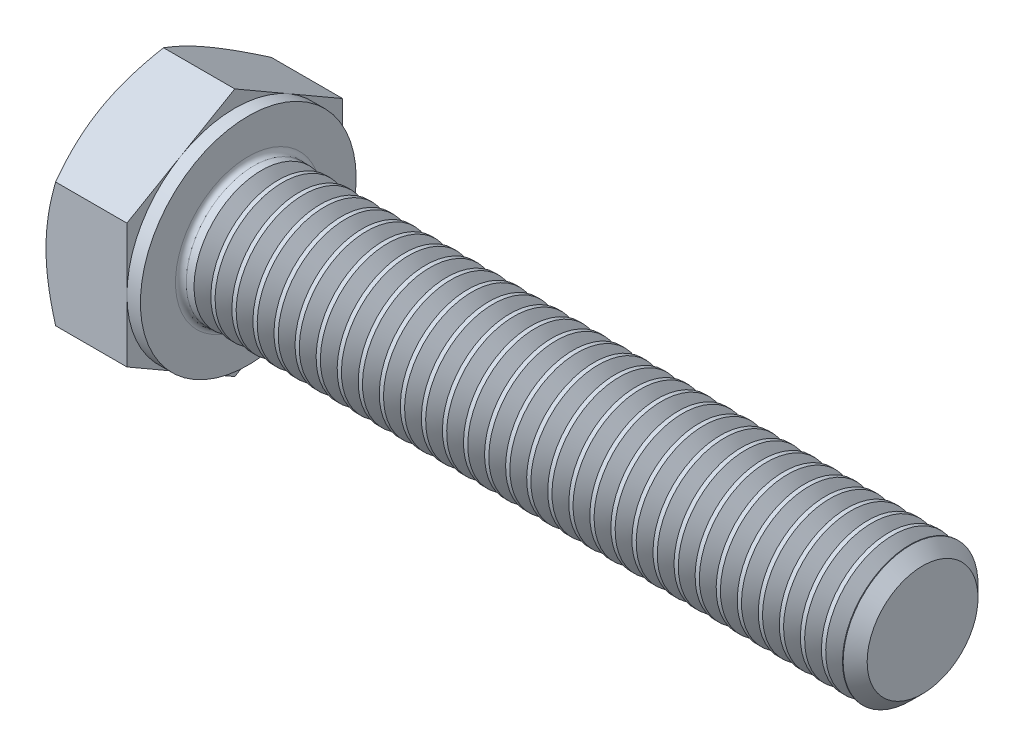
SolidWorks part; units mm, degrees
ref_plane "Plane1" through (0, 0, 0) normal (0, 0, 1) x (1, 0, 0)
ref_plane "Plane2" through (0, 0, 0) normal (0, 1, 0) x (1, 0, 0)
ref_plane "Plane3" through (0, 0, 0) normal (1, 0, 0) x (0, 0, -1)
sketch "Sketch1" plane through (0, 0, 0) normal (1, 0, 0) x (0, 0, -1)
  line L0 (4, 2.3094) -> (4, -2.3094)
  line L1 (-4, 2.3094) -> (-4, -2.3094)
  line L2 (4, -2.3094) -> (0, -4.6188)
  line L3 (0, -4.6188) -> (-4, -2.3094)
  line L4 (4, 2.3094) -> (0, 4.6188)
  line L5 (0, 4.6188) -> (-4, 2.3094)
  dimension "Width_flats" = 8
  dimension "D2" = 120
  dimension "D3" = 4
  dimension "D4" = 4
  dimension "D5" = 4
extrude "BaseHead" add sketch "Sketch1" along normal blind 3.5
sketch "BodySke" plane through (0, 0, 0) normal (0, 0, 1) x (1, 0, 0)
  line L0 (0, 2.3094) -> (0, -2.3094) construction
  line L1 (0, 0) -> (28.5, 0)
  line L2 (0, 0) -> (0, 2.5)
  line L3 (0, 2.5) -> (28.055, 2.5)
  line L4 (28.5, 0) -> (28.5, 2.055)
  line L5 (3.5, 4.6188) -> (3.5, 2.3094) construction
  line L6 (28.5, 2.055) -> (28.055, 2.5)
  line L7 (0, 0) -> (96.52, 0) construction
  line L8 (28.5, -2.055) -> (28.055, -2.5) construction
  line L9 (0, -2.5) -> (28.055, -2.5) construction
  line L10 (4.3, 15.24) -> (4.3, -1.27) construction
  line L11 (3.5, 15.24) -> (3.5, -1.27) construction
  line L12 (3.5, 2.3094) -> (3.5, -2.3094) construction
  dimension "Length" = 25
  dimension "Body_ch_ang" = 45
  dimension "Diameter" = 5
  dimension "Minor_dia" = 4.11
  dimension "Advance" = 0.8
  dimension "Thread_nom" = 25
revolve "BaseBody" add sketch "BodySke"
cosmetic thread "ThreadCosmetic" [suppressed]
fillet "HeadFillet" radius 0.2 1 edges at (3.5, 0, -2.5)
sketch "Sketch3" plane through (0, 0, 0) normal (0, 0, 1) x (1, 0, 0)
  line L0 (0, 4) -> (3.244, 9.6188)
  line L1 (0, 4.6188) -> (0, 2.3094) construction
  line L2 (3.244, 9.6188) -> (3.244, 14.6188)
  line L3 (3.244, 14.6188) -> (-10, 14.6188)
  line L4 (-10, 14.6188) -> (-10, 4)
  line L5 (-10, 4) -> (0, 4)
  line L6 (0, 0) -> (99.06, 0) construction
  line L7 (3.5, 4.6188) -> (0, 4.6188) construction
  dimension "D1" = 4
  dimension "D2" = 5
  dimension "D3" = 10
  dimension "D4" = 5
  dimension "Head_ch_ang" = 30
revolve "HeadChamfer" cut sketch "Sketch3" angle 360 about L6
sketch "Sketch4" plane through (0, 0, 0) normal (0, 0, 1) x (1, 0, 0)
  line L1 (3.5, 4.6188) -> (3.5, 2.3094) construction
  line L2 (3.5, 4) -> (3, 4)
  line L3 (3.5, 4) -> (3.5, 14.6188)
  line L4 (3.5, 14.6188) -> (3, 14.6188)
  line L5 (0, 0) -> (95.25, 0) construction
  line L6 (0, 0) -> (96.52, 0) construction
  line L7 (3, 4) -> (3, 14.6188)
  line L8 (3.5, 4.6188) -> (0.3573, 4.6188) construction
  dimension "D1" = 8
  dimension "D2" = 10
  dimension "Bearing_ht" = 0.5
revolve "BearingFace" cut sketch "Sketch4" angle 360 about L5
sketch "ThdSchSke" plane through (0, 0, 0) normal (0, 0, 1) x (1, 0, 0)
  line L0 (4.3, -2.055) -> (3.9884, -2.5)
  line L1 (4.3, -2.055) -> (4.6116, -2.5)
  line L2 (4.6116, -2.5) -> (4.6116, -3.125)
  line L3 (-3.175, 0) -> (5.1513, 0) construction
  line L5 (4.6116, -3.125) -> (3.9884, -3.125)
  line L6 (3.9884, -3.125) -> (3.9884, -2.5)
  dimension "Thread_minor" = 4.11
  dimension "Diameter" = 5
  dimension "Start" = 4.3
  dimension "SideAngle" = 55
  dimension "VeeAngle" = 70
  dimension "Overcut" = 6.25
revolve "ThreadSchematic" cut sketch "ThdSchSke" angle 360 about L3
pattern_linear "ThdSchPat" count 31 spacing 0.7806 along (1, 0, 0) of "ThreadSchematic"
equation "\"D3@Sketch1\" = \"Width_flats@Sketch1\" / 2"
equation "\"D4@Sketch1\" = \"D3@Sketch1\""
equation "\"D5@Sketch1\" = \"D4@Sketch1\""
equation "\"Thread_minor@ThreadCosmetic\" = \"Minor_dia@BodySke\""
equation "\"D1@Sketch3\" = \"Width_flats@Sketch1\" / 2"
equation "\"D1@Sketch4\" = \"Width_flats@Sketch1\""
equation "\"Thread_length@ThreadCosmetic\" = ((sgn( (\"Length@BodySke\" - \"Advance@BodySke\" ) - \"Thread_nom@BodySke\" )-1)*( (\"Length@BodySke\" - \"Advance@BodySke\" ) - \"Thread_nom@BodySke\" ))/-2+ \"Thread_nom@BodySke\""
equation "\"Thread_minor@ThdSchSke\" = \"Minor_dia@BodySke\""
equation "\"Diameter@ThdSchSke\" = \"Diameter@BodySke\""
equation "\"Overcut@ThdSchSke\" = \"Diameter@BodySke\" * 1.25"
equation "\"Start@ThdSchSke\" = \"Head_ht@BaseHead\" + \"Length@BodySke\" - \"Thread_length@ThreadCosmetic\"  '---Non-countersunk---"
equation "\"Num_threads@ThdSchPat\" = int( \"Thread_length@ThreadCosmetic\" / \"Advance@BodySke\" + 0.999 )  + 1"
equation "\"Advance@ThdSchPat\" = \"Thread_length@ThreadCosmetic\" /  (\"Num_threads@ThdSchPat\" - 1) 'relax it"
equation "\"Num_threads@ThdSchPat\" = \"Num_threads@ThdSchPat\" - sgn( \"Num_threads@ThdSchPat\" - 1) '---chamfered tips only---"
